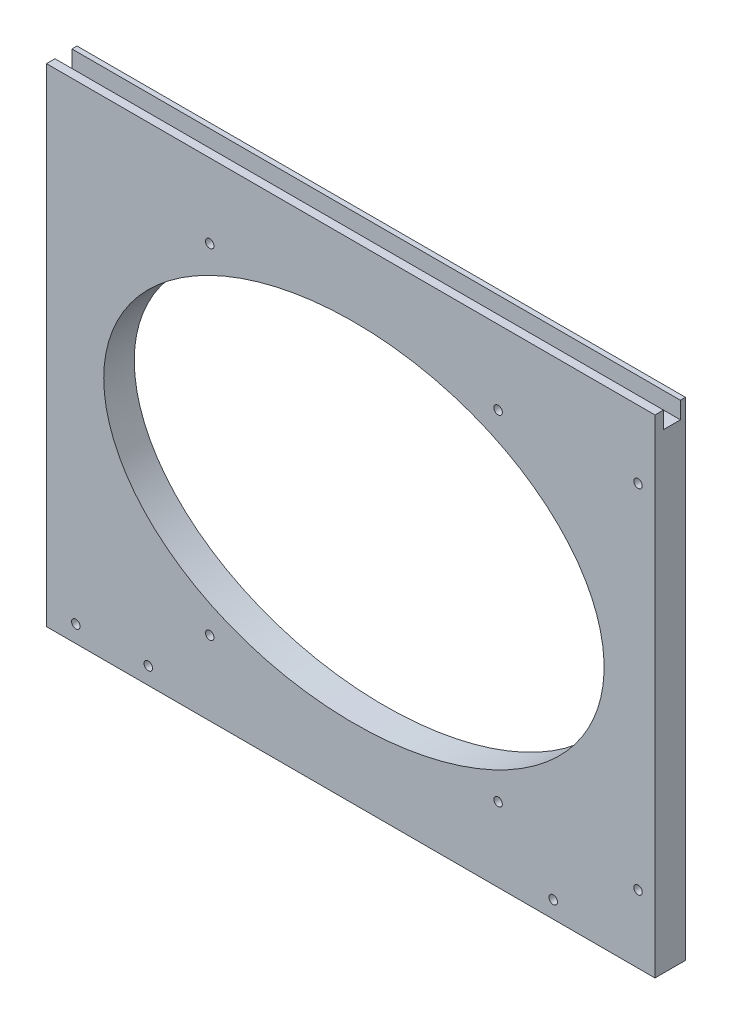
SolidWorks part; units mm, degrees
material "Pine"
ref_plane "Front Plane" through (0, 0, 0) normal (0, 0, 1) x (1, 0, 0)
ref_plane "Top Plane" through (0, 0, 0) normal (0, 1, 0) x (1, 0, 0)
ref_plane "Right Plane" through (0, 0, 0) normal (1, 0, 0) x (0, 0, -1)
sketch "Sketch1" plane through (0, 0, 0) normal (0, 0, 1) x (1, 0, 0)
  line L0 (-5300.6625, 1520.825) -> (-5451.475, 1520.825)
  line L1 (-5456.2375, 1384.3) -> (-5456.2375, 1516.0625)
  line L2 (-5557.8375, 1546.225) -> (-5194.3, 1546.225)
  line L3 (-5557.8375, 1539.875) -> (-5194.3, 1539.875)
  line L4 (-5297.4875, 1377.95) -> (-5454.65, 1377.95)
  line L5 (-5291.1375, 1384.3) -> (-5291.1375, 1516.0625)
  line L6 (-5300.6625, 1525.5875) -> (-5451.475, 1525.5875)
  line L7 (-5461, 1384.3) -> (-5461, 1516.0625)
  line L8 (-5297.4875, 1382.7125) -> (-5454.65, 1382.7125)
  line L9 (-5295.9, 1384.3) -> (-5295.9, 1516.0625)
  line L10 (-5740.4, 998.5375) -> (-5740.4, 1181.1)
  line L11 (-5740.4, 1181.1) -> (-5512.5938, 1181.1)
  line L12 (-5512.5938, 1181.1) -> (-5512.5938, 998.5375)
  line L13 (-5512.5938, 998.5375) -> (-5740.4, 998.5375)
  line L14 (-5258.5938, 1181.1) -> (-5486.4, 1181.1)
  line L15 (-5258.5938, 998.5375) -> (-5258.5938, 1181.1)
  line L16 (-5486.4, 998.5375) -> (-5258.5938, 998.5375)
  line L17 (-5486.4, 1181.1) -> (-5486.4, 998.5375)
  line L18 (-5740.4, 898.525) -> (-5011.7375, 898.525)
  line L19 (-5168.1062, 1384.3) -> (-5168.1062, 1392.2375)
  line L20 (-5176.0437, 1400.175) -> (-5245.8937, 1400.175)
  line L21 (-5253.8313, 1392.2375) -> (-5253.8313, 1384.3)
  line L22 (-5451.475, 1512.8875) -> (-5451.475, 1384.3)
  line L23 (-5303.8375, 1516.0625) -> (-5448.3, 1516.0625)
  line L24 (-5498.3062, 1384.3) -> (-5451.475, 1384.3)
  line L25 (-5253.8313, 1384.3) -> (-5300.6625, 1384.3)
  line L26 (-5584.0312, 1384.3) -> (-5740.4, 1384.3)
  line L27 (-5564.1875, 1536.7) -> (-5740.4, 1536.7)
  line L28 (-5740.4, 1357.3125) -> (-5740.4, 1206.5)
  line L29 (-5011.7375, 1357.3125) -> (-5740.4, 1357.3125)
  line L30 (-5011.7375, 1206.5) -> (-5011.7375, 1357.3125)
  line L31 (-5740.4, 1206.5) -> (-5011.7375, 1206.5)
  line L32 (-4765.675, 1549.4) -> (-4978.4, 1549.4)
  line L33 (-4765.675, 1397) -> (-4765.675, 1549.4)
  line L34 (-4978.4, 1397) -> (-4765.675, 1397)
  line L35 (-4978.4, 1549.4) -> (-4978.4, 1397)
  line L36 (-4765.675, 1371.6) -> (-4978.4, 1371.6)
  line L37 (-4765.675, 1219.2) -> (-4765.675, 1371.6)
  line L38 (-4978.4, 1219.2) -> (-4765.675, 1219.2)
  line L39 (-4978.4, 1371.6) -> (-4978.4, 1219.2)
  line L40 (-5284.7875, 803.275) -> (-5272.0875, 803.275)
  line L41 (-5187.95, 1536.7) -> (-5011.7375, 1536.7)
  line L42 (-5300.6625, 1384.3) -> (-5300.6625, 1512.8875)
  line L43 (-5740.4, 1536.7) -> (-5740.4, 1384.3)
  line L44 (-5557.8375, 1536.7) -> (-5557.8375, 1549.4)
  line L45 (-5557.8375, 1549.4) -> (-5194.3, 1549.4)
  line L46 (-5194.3, 1549.4) -> (-5194.3, 1536.7)
  line L47 (-5011.7375, 1536.7) -> (-5011.7375, 1384.3)
  line L48 (-5011.7375, 1384.3) -> (-5168.1062, 1384.3)
  line L49 (-5498.3062, 1384.3) -> (-5498.3062, 1392.2375)
  line L50 (-5506.2437, 1400.175) -> (-5576.0938, 1400.175)
  line L51 (-5584.0312, 1392.2375) -> (-5584.0312, 1384.3)
  line L52 (-5740.4, 660.4) -> (-5740.4, 898.525)
  line L53 (-5011.7375, 898.525) -> (-5011.7375, 660.4)
  line L54 (-5011.7375, 660.4) -> (-5740.4, 660.4)
  line L55 (-5291.1375, 803.275) -> (-5291.1375, 752.475)
  line L56 (-5265.7375, 752.475) -> (-5265.7375, 803.275)
  line L57 (-5284.7875, 752.475) -> (-5272.0875, 752.475)
  arc A0 (-5451.475, 1520.825) -> (-5456.2375, 1516.0625) centre (-5451.475, 1516.0625) ccw
  arc A1 (-5461, 1384.3) -> (-5454.65, 1377.95) centre (-5454.65, 1384.3) ccw
  arc A2 (-5297.4875, 1377.95) -> (-5291.1375, 1384.3) centre (-5297.4875, 1384.3) ccw
  circle A3 centre (-5037.9312, 1233.4875) radius 1.5875
  circle A4 centre (-5037.9312, 1328.7375) radius 1.5875
  circle A5 centre (-5714.2063, 1233.4875) radius 1.5875
  circle A6 centre (-5714.2063, 1328.7375) radius 1.5875
  circle A7 centre (-5018.0875, 1333.5) radius 1.5875
  circle A8 centre (-5018.0875, 1231.9) radius 1.5875
  circle A9 centre (-5734.05, 1231.9) radius 1.5875
  circle A10 centre (-5734.05, 1333.5) radius 1.5875
  circle A11 centre (-5734.05, 1511.3) radius 1.5875
  circle A12 centre (-5734.05, 1409.7) radius 1.5875
  circle A13 centre (-5018.0875, 1511.3) radius 1.5875
  circle A14 centre (-5018.0875, 1409.7) radius 1.5875
  arc A15 (-5557.8375, 1546.225) -> (-5557.8375, 1539.875) centre (-5557.8375, 1543.05) ccw
  arc A16 (-5194.3, 1539.875) -> (-5194.3, 1546.225) centre (-5194.3, 1543.05) ccw
  arc A17 (-5291.1375, 1516.0625) -> (-5300.6625, 1525.5875) centre (-5300.6625, 1516.0625) ccw
  arc A18 (-5451.475, 1525.5875) -> (-5461, 1516.0625) centre (-5451.475, 1516.0625) ccw
  arc A19 (-5456.2375, 1384.3) -> (-5454.65, 1382.7125) centre (-5454.65, 1384.3) ccw
  arc A20 (-5297.4875, 1382.7125) -> (-5295.9, 1384.3) centre (-5297.4875, 1384.3) ccw
  arc A21 (-5295.9, 1516.0625) -> (-5300.6625, 1520.825) centre (-5300.6625, 1516.0625) ccw
  circle A22 centre (-5702.3, 892.175) radius 1.5875
  circle A23 centre (-5734.05, 860.425) radius 1.5875
  circle A24 centre (-5474.8906, 892.175) radius 1.5875
  circle A25 centre (-5277.2469, 892.175) radius 1.5875
  circle A26 centre (-5049.8375, 892.175) radius 1.5875
  circle A27 centre (-5018.0875, 860.425) radius 1.5875
  circle A28 centre (-5296.6938, 1174.75) radius 1.5875
  circle A29 centre (-5448.3, 1174.75) radius 1.5875
  circle A30 centre (-5264.9437, 1155.7) radius 1.5875
  circle A31 centre (-5264.9437, 1023.9375) radius 1.5875
  circle A32 centre (-5518.9438, 1155.7) radius 1.5875
  circle A33 centre (-5518.9438, 1023.9375) radius 1.5875
  circle A34 centre (-5702.3, 1004.8875) radius 1.5875
  circle A35 centre (-5550.6937, 1004.8875) radius 1.5875
  arc A36 (-5576.0938, 1400.175) -> (-5584.0312, 1392.2375) centre (-5576.0938, 1392.2375) ccw
  arc A37 (-5168.1062, 1392.2375) -> (-5176.0437, 1400.175) centre (-5176.0437, 1392.2375) ccw
  arc A38 (-5245.8937, 1400.175) -> (-5253.8313, 1392.2375) centre (-5245.8937, 1392.2375) ccw
  arc A39 (-5448.3, 1516.0625) -> (-5451.475, 1512.8875) centre (-5448.3, 1512.8875) ccw
  arc A40 (-5284.7875, 803.275) -> (-5291.1375, 803.275) centre (-5287.9625, 803.275) ccw
  circle A41 centre (-5679.2812, 1026.3187) radius 1.5875
  circle A42 centre (-5679.2812, 1153.3187) radius 1.5875
  circle A43 centre (-5571.3313, 1153.3187) radius 1.5875
  circle A44 centre (-5571.3313, 1026.3187) radius 1.5875
  circle A45 centre (-5317.3312, 1153.3187) radius 1.5875
  circle A46 centre (-5317.3312, 1026.3187) radius 1.5875
  circle A47 centre (-5425.2812, 1026.3187) radius 1.5875
  circle A48 centre (-5425.2812, 1153.3187) radius 1.5875
  arc A49 (-5194.3, 1536.7) -> (-5187.95, 1536.7) centre (-5191.125, 1536.7) ccw
  arc A50 (-5564.1875, 1536.7) -> (-5557.8375, 1536.7) centre (-5561.0125, 1536.7) ccw
  arc A51 (-5300.6625, 1512.8875) -> (-5303.8375, 1516.0625) centre (-5303.8375, 1512.8875) ccw
  arc A52 (-5498.3062, 1392.2375) -> (-5506.2437, 1400.175) centre (-5506.2437, 1392.2375) ccw
  circle A53 centre (-5712.46, 784.225) radius 4.7625
  arc A54 (-5272.0875, 752.475) -> (-5265.7375, 752.475) centre (-5268.9125, 752.475) ccw
  arc A55 (-5291.1375, 752.475) -> (-5284.7875, 752.475) centre (-5287.9625, 752.475) ccw
  circle A56 centre (-5182.3938, 684.2125) radius 3.175
  circle A57 centre (-5239.5437, 684.2125) radius 3.175
  circle A58 centre (-5512.5938, 684.2125) radius 3.175
  circle A59 centre (-5569.7437, 684.2125) radius 3.175
  circle A60 centre (-5474.8906, 666.75) radius 1.5875
  circle A61 centre (-5277.2469, 666.75) radius 1.5875
  circle A62 centre (-5734.05, 698.5) radius 1.5875
  circle A63 centre (-5702.3, 666.75) radius 1.5875
  circle A64 centre (-5049.8375, 666.75) radius 1.5875
  circle A65 centre (-5018.0875, 698.5) radius 1.5875
  circle A66 centre (-5713.73, 835.025) radius 4.7625
  circle A67 centre (-5712.46, 819.785) radius 4.7625
  circle A68 centre (-5712.46, 802.005) radius 4.7625
  circle A69 centre (-5714.2063, 1314.45) radius 3.175
  circle A70 centre (-5037.9312, 1314.45) radius 3.175
  arc A71 (-5265.7375, 803.275) -> (-5272.0875, 803.275) centre (-5268.9125, 803.275) ccw
  ellipse E0 centre (-5371.3062, 1089.8188) end of major axis (-5277.6438, 1089.8188) minor radius 65.0875
  ellipse E1 centre (-5625.3062, 1089.8188) end of major axis (-5531.6438, 1089.8188) minor radius 65.0875
sketch "SpeakerMounting" plane through (0, 0, 0) normal (0, 0, 1) x (1, 0, 0)
  line L0 (-5512.5938, 998.5375) -> (-5512.5938, 1181.1)
  line L1 (-5512.5938, 1181.1) -> (-5740.4, 1181.1)
  line L2 (-5740.4, 1181.1) -> (-5740.4, 998.5375)
  line L3 (-5740.4, 998.5375) -> (-5512.5938, 998.5375)
extrude "SpeakerMounting_Thickness" add sketch "SpeakerMounting" against normal blind 11.43
sketch "SpeakerCutout" plane through (0, 0, 0) normal (0, 0, 1) x (1, 0, 0)
  line L0 (-5625.3062, 1154.9062) -> (-5625.3062, 1024.7313) construction
  line L1 (-5718.9687, 1089.8188) -> (-5531.6438, 1089.8188) construction
  circle A0 centre (-5571.3313, 1153.3187) radius 1.5875
  circle A1 centre (-5518.9438, 1155.7) radius 1.5875
  circle A2 centre (-5518.9438, 1023.9375) radius 1.5875
  circle A3 centre (-5550.6937, 1004.8875) radius 1.5875
  circle A4 centre (-5571.3313, 1026.3187) radius 1.5875
  circle A5 centre (-5679.2812, 1026.3187) radius 1.5875
  circle A6 centre (-5702.3, 1004.8875) radius 1.5875
  circle A7 centre (-5679.2812, 1153.3187) radius 1.5875
  ellipse E0 centre (-5625.3062, 1089.8188) end of major axis (-5718.9687, 1089.8188) minor radius 65.0875
extrude "Cut-Extrude1" cut sketch "SpeakerCutout" against normal up to surface (11.43 mm away) up to face at (-5626.4969, 1089.8188, -11.43)
sketch "SpeakerSlotForScreen" plane through (-5512.5938, 0, 0) normal (1, 0, 0) x (0, 0, -1)
  line L0 (5.715, 1181.1) -> (3.175, 1181.1)
  line L1 (11.43, 1181.1) -> (0, 1181.1) construction
  line L2 (3.175, 1181.1) -> (3.175, 1174.75)
  line L3 (3.175, 1174.75) -> (9.525, 1174.75)
  line L4 (9.525, 1174.75) -> (9.525, 1181.1)
  line L5 (9.525, 1181.1) -> (5.715, 1181.1)
extrude "Cut-Extrude2" cut sketch "SpeakerSlotForScreen" against normal up to surface (227.8063 mm away) up to face at (-5740.4, 1089.8188, -5.715)
sketch "Sketch2" plane through (0, 0, -11.43) normal (0, 0, -1) x (-1, 0, 0)
  circle A0 centre (5729.4335, 1004.8875) radius 1.5875
extrude "Cut-Extrude3" cut sketch "Sketch2" against normal up to surface (11.43 mm away) up to face at (-5677.6937, 1153.3187, 0)
